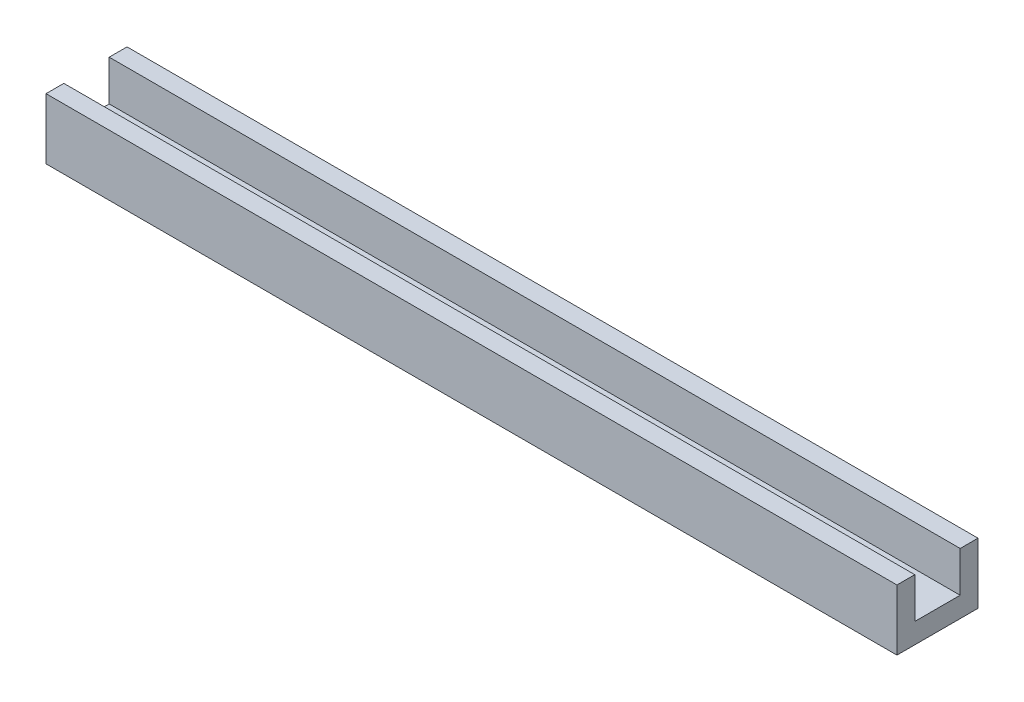
SolidWorks part; units mm, degrees
ref_plane "Front Plane" through (0, 0, 0) normal (0, 0, 1) x (1, 0, 0)
ref_plane "Top Plane" through (0, 0, 0) normal (0, 1, 0) x (1, 0, 0)
ref_plane "Right Plane" through (0, 0, 0) normal (1, 0, 0) x (0, 0, -1)
sketch "Sketch1" plane through (0, 0, 0) normal (0, 1, 0) x (1, 0, 0)
  line L1 (0, 0) -> (210, 0)
  line L2 (0, 0) -> (0, 20)
  line L3 (0, 20) -> (210, 20)
  line L4 (210, 0) -> (210, 20)
  dimension "D1" = 210
  dimension "D2" = 20
extrude "Boss-Extrude1" add sketch "Sketch1" along normal blind 15
sketch "Sketch2" plane through (0, 15, 0) normal (0, 1, 0) x (1, 0, 0)
  line L0 (0, 20) -> (0, 0) construction
  line L1 (0, 5) -> (210, 5)
  line L2 (0, 5) -> (0, 15)
  line L3 (0, 15) -> (210, 15)
  line L4 (210, 5) -> (210, 15)
  line L5 (210, 0) -> (210, 20) construction
  dimension "D1" = 5
  dimension "D2" = 5
extrude "Cut-Extrude1" cut sketch "Sketch2" against normal blind 10
sketch "Sketch3" plane through (0, 5, 0) normal (0, 1, 0) x (1, 0, 0)
  line L0 (0, 0) -> (210, 0) construction
  line L1 (0, 15) -> (0, 5) construction
  circle A0 centre (25, 10) radius 1.8
  dimension "D2" = 25
  dimension "D3" = 3.6
  dimension "D1" = 10
extrude "Cut-Extrude2" cut sketch "Sketch3" against normal through all
sketch "Sketch5" plane through (0, 5, 0) normal (0, 1, 0) x (1, 0, 0)
  circle A0 centre (25, 10) radius 3.5
  dimension "D1" = 7
extrude "Cut-Extrude3" cut sketch "Sketch5" against normal blind 3.6
ref_plane "Plane1" through (58.6119, 0, 0) normal (1, 0, 0) x (0, 0, -1)
mirror "Mirror2" about plane through (58.6119, 0, 0) normal (1, 0, 0) of "Cut-Extrude3", "Cut-Extrude2"
sketch "Sketch6" plane through (0, 0, -15) normal (0, 0, 1) x (1, 0, 0)
  line L0 (210, 15) -> (0, 15) construction
  line L1 (210, 5) -> (0, 5)
  line L2 (210, 5) -> (210, 15)
  line L3 (210, 15) -> (0, 15)
  line L4 (0, 5) -> (0, 15)
extrude "Cut-Extrude4" cut sketch "Sketch6" against normal blind 0.6
sketch "Sketch7" plane through (0, 0, -5) normal (0, 0, -1) x (-1, 0, 0)
  line L1 (-210, 15) -> (0, 15)
  line L2 (-210, 15) -> (-210, 5)
  line L3 (-210, 5) -> (0, 5)
  line L4 (0, 15) -> (0, 5)
extrude "Cut-Extrude5" cut sketch "Sketch7" against normal blind 0.6
